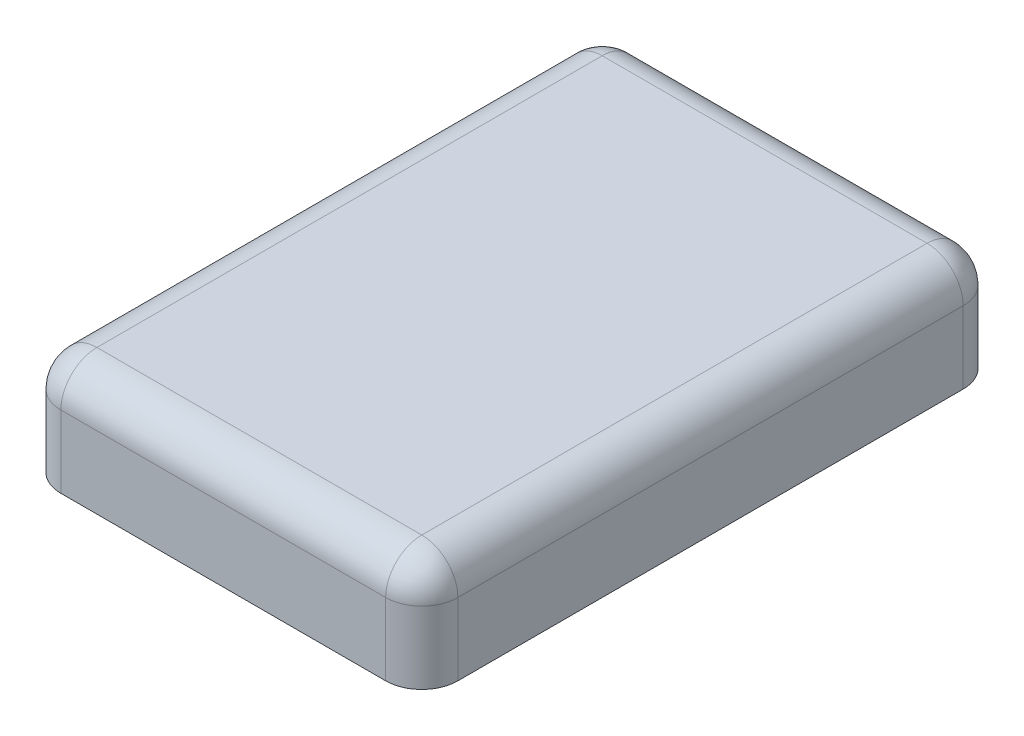
SolidWorks part; units mm, degrees
ref_plane "Front Plane" through (0, 0, 0) normal (0, 0, 1) x (1, 0, 0)
ref_plane "Top Plane" through (0, 0, 0) normal (0, 1, 0) x (1, 0, 0)
ref_plane "Right Plane" through (0, 0, 0) normal (1, 0, 0) x (0, 0, -1)
sketch "BaseS" plane through (0, 0, 0) normal (0, 1, 0) x (1, 0, 0)
  line L1 (-1.1, 1.6) -> (1.1, 1.6)
  line L2 (-1.1, 1.6) -> (-1.1, -1.6)
  line L3 (-1.1, -1.6) -> (1.1, -1.6)
  line L4 (1.1, 1.6) -> (1.1, -1.6)
  line L5 (-1.1, 1.6) -> (1.1, -1.6) construction
  line L6 (-1.1, -1.6) -> (1.1, 1.6) construction
  point P0 (0, 0)
  dimension "Width" = 2.2
  dimension "Length" = 3.2
extrude "Base" add sketch "BaseS" along normal blind 0.6
fillet "SideF" radius 0.2 4 edges at (1.1, 0.3, 1.6) (1.1, 0.3, -1.6) (-1.1, 0.3, 1.6) (-1.1, 0.3, -1.6)
fillet "TopF" radius 0.2 8 edges at (-1.0414, 0.6, 1.5414) (-1.1, 0.6, 0) (-1.0414, 0.6, -1.5414) (0, 0.6, -1.6) (1.0414, 0.6, -1.5414) (1.1, 0.6, 0) (1.0414, 0.6, 1.5414) (0, 0.6, 1.6)
